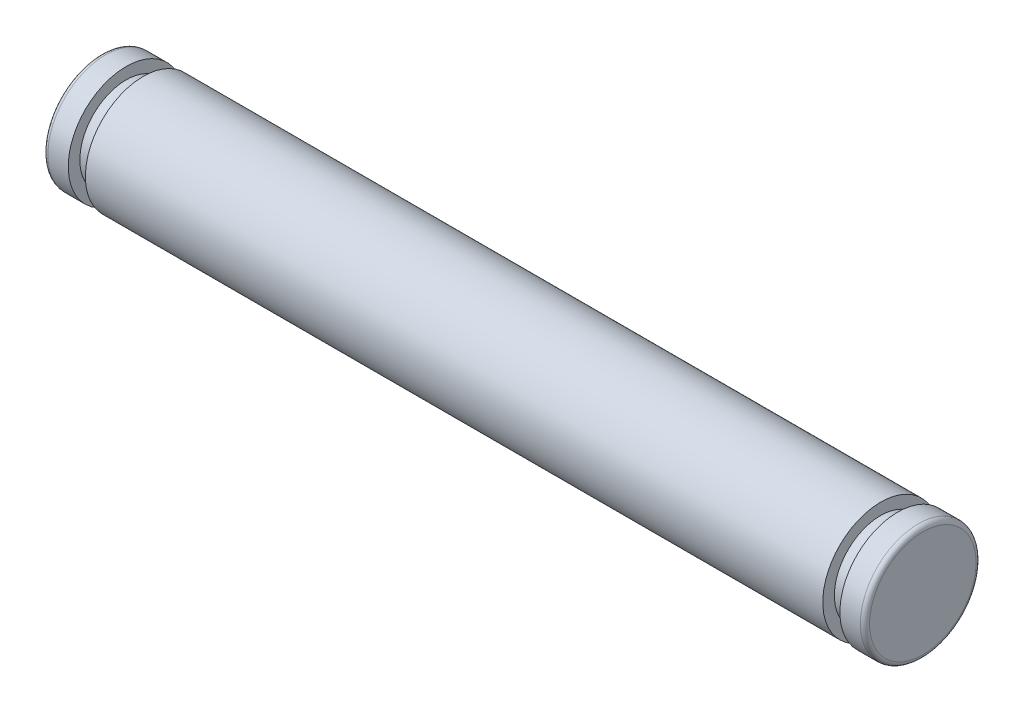
SolidWorks part; units mm, degrees
ref_plane "Front Plane" through (0, 0, 0) normal (0, 0, 1) x (1, 0, 0)
ref_plane "Top Plane" through (0, 0, 0) normal (0, 1, 0) x (1, 0, 0)
ref_plane "Right Plane" through (0, 0, 0) normal (1, 0, 0) x (0, 0, -1)
sketch "Sketch1" plane through (0, 0, 0) normal (0, 1, 0) x (1, 0, 0)
  line L0 (-17.75, 0) -> (0, 0) construction
  line L1 (0, 0) -> (17.75, 0) construction
  line L2 (0, 0) -> (0, 4.0847) construction
  line L3 (-15.927, 2.5) -> (15.927, 2.5)
  line L4 (15.927, 2.5) -> (15.927, 2)
  line L5 (15.927, 2) -> (16.667, 2)
  line L6 (16.667, 2) -> (16.667, 2.5)
  line L7 (16.667, 2.5) -> (17.55, 2.5)
  line L8 (17.75, 2.3) -> (17.75, 0)
  line L9 (-17.75, 2.3) -> (-17.75, 0)
  line L10 (-16.667, 2.5) -> (-17.55, 2.5)
  line L11 (-16.667, 2) -> (-16.667, 2.5)
  line L12 (-15.927, 2) -> (-16.667, 2)
  line L13 (-15.927, 2.5) -> (-15.927, 2)
  line L14 (17.75, 0) -> (-17.75, 0)
  arc A0 (17.55, 2.5) -> (17.75, 2.3) centre (17.55, 2.3) cw
  arc A1 (-17.75, 2.3) -> (-17.55, 2.5) centre (-17.55, 2.3) cw
  point P8 (0, 2.5)
  point P14 (17.75, 2.5)
  point P21 (-17.75, 2.5)
  dimension "D6" = 0.2
  dimension "D1" = 31.854
  dimension "D2" = 2.5
  dimension "D3" = 2
  dimension "D4" = 0.74
  dimension "D5" = 35.5
revolve "Revolve1" add sketch "Sketch1" angle 360 about L14
